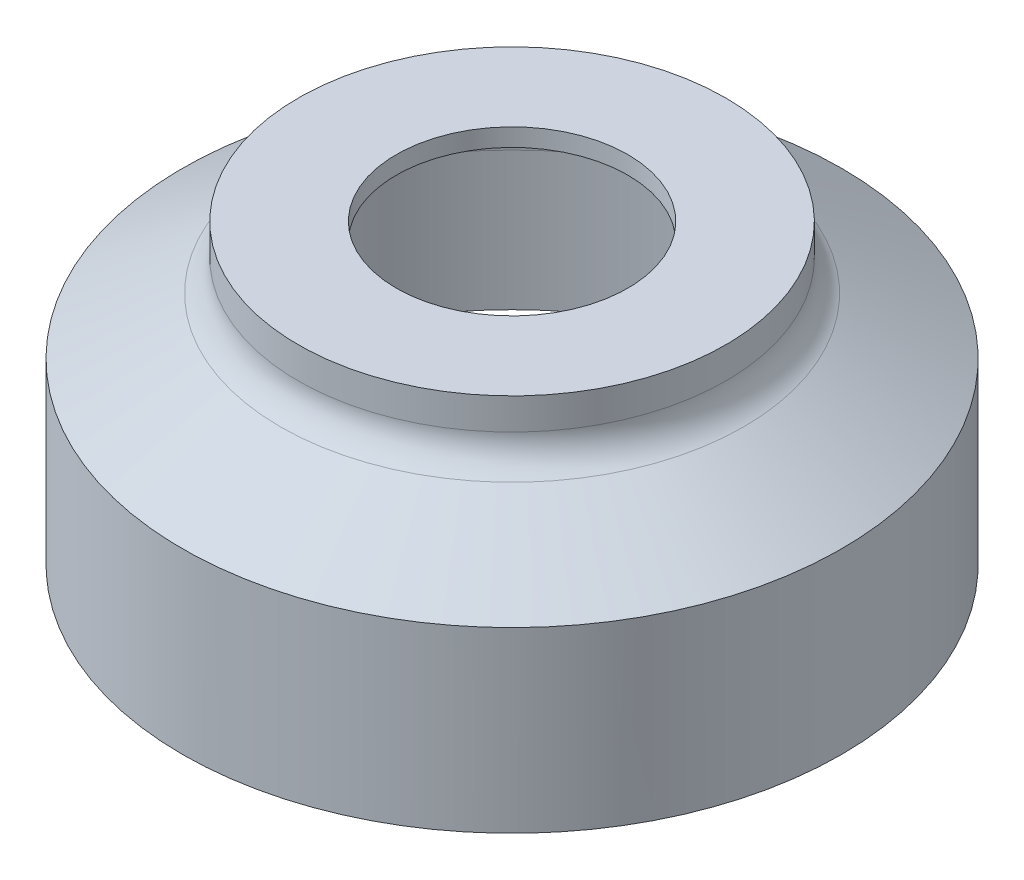
SolidWorks part; units mm, degrees
material "Alloy Steel"
ref_plane "Front Plane" through (0, 0, 0) normal (0, 0, 1) x (1, 0, 0)
ref_plane "Top Plane" through (0, 0, 0) normal (0, 1, 0) x (1, 0, 0)
ref_plane "Right Plane" through (0, 0, 0) normal (1, 0, 0) x (0, 0, -1)
sketch "Sketch1" plane through (0, 0, 0) normal (0, 1, 0) x (1, 0, 0)
  circle A0 centre (0, 0) radius 14.097
  dimension "D1" = 28.194
extrude "Boss-Extrude1" add sketch "Sketch1" along normal blind 12.7
sketch "Sketch2" plane through (0, 0, 0) normal (0, 0, 1) x (1, 0, 0)
  line L0 (4.953, 12.7) -> (4.953, 11.938)
  line L1 (14.097, 12.7) -> (-14.097, 12.7) construction
  line L2 (4.953, 11.938) -> (8.382, 11.938)
  line L3 (8.382, 11.938) -> (8.382, 9.652)
  line L4 (8.382, 9.652) -> (12.573, 7.2323)
  line L5 (13.335, 5.9125) -> (13.335, 0)
  line L6 (-14.097, 0) -> (14.097, 0) construction
  line L7 (13.335, 0) -> (0, 0)
  line L8 (0, 0) -> (0, 12.7)
  line L9 (0, 12.7) -> (4.953, 12.7)
  line L10 (0, 0) -> (0, 15.9249) construction
  arc A0 (12.573, 7.2323) -> (13.335, 5.9125) centre (11.811, 5.9125) cw
  dimension "D7" = 1.524
  dimension "D1" = 9.906
  dimension "D2" = 16.764
  dimension "D3" = 26.67
  dimension "D4" = 2.286
  dimension "D5" = 0.762
  dimension "D6" = 60
revolve "Cut-Revolve1" cut sketch "Sketch2" angle 360 about L10
sketch "Sketch3" plane through (0, 0, 0) normal (0, 0, 1) x (1, 0, 0)
  line L0 (0, 0) -> (0, 13.334) construction
  line L1 (14.097, 12.7) -> (14.097, 7.62)
  line L2 (14.097, 7.62) -> (9.906, 10.0397)
  line L3 (9.144, 11.3595) -> (9.144, 12.7)
  line L4 (14.097, 12.7) -> (-14.097, 12.7) construction
  line L5 (9.144, 12.7) -> (14.097, 12.7)
  line L6 (-14.097, 0) -> (14.097, 0) construction
  arc A0 (9.144, 11.3595) -> (9.906, 10.0397) centre (10.668, 11.3595) ccw
  dimension "D1" = 1.524
  dimension "D2" = 7.62
  dimension "D3" = 60
  dimension "D4" = 18.288
revolve "Cut-Revolve2" cut sketch "Sketch3" angle 360 about L0
